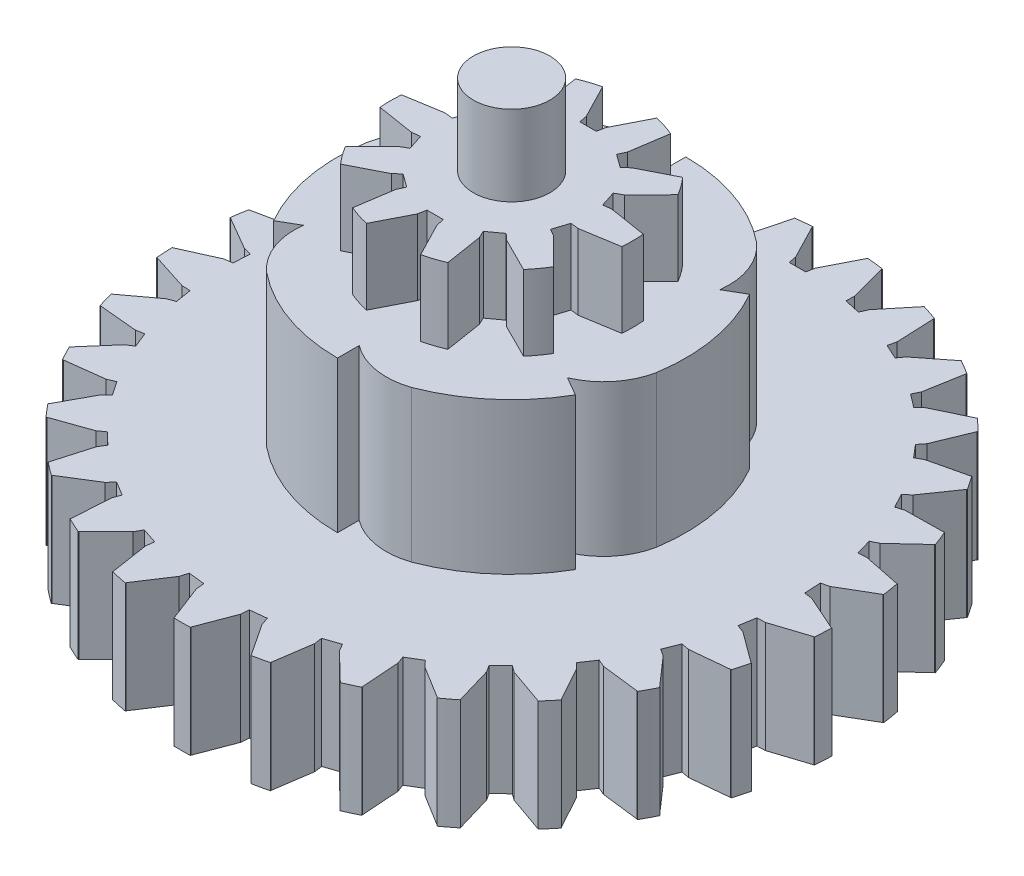
SolidWorks part; units mm, degrees
ref_plane "Front Plane" through (0, 0, 0) normal (0, 0, 1) x (1, 0, 0)
ref_plane "Top Plane" through (0, 0, 0) normal (0, 1, 0) x (1, 0, 0)
ref_plane "Right Plane" through (0, 0, 0) normal (1, 0, 0) x (0, 0, -1)
sketch "Sketch1" plane through (0, 0, 0) normal (0, 1, 0) x (1, 0, 0)
  circle A0 centre (-83.1207, 52.7325) radius 4.5085
extrude "Boss-Extrude1" add sketch "Sketch1" along normal blind 2.794
sketch "Sketch2" plane through (0, 2.794, 0) normal (0, 1, 0) x (1, 0, 0)
  circle A0 centre (-83.1207, 52.7325) radius 1.4224
extrude "Boss-Extrude2" add sketch "Sketch2" along normal blind 2.9845
sketch "Sketch3" plane through (0, 2.794, 0) normal (0, 1, 0) x (1, 0, 0)
  line L0 (-83.1207, 55.5745) -> (-82.8159, 55.5745)
  line L1 (-83.1207, 55.5745) -> (-83.4255, 55.5745)
  line L2 (-83.4255, 55.5745) -> (-83.4853, 55.8734)
  line L3 (-82.8159, 55.5745) -> (-82.7574, 55.8745)
  line L4 (-82.7574, 55.8745) -> (-82.1099, 57.1432)
  line L5 (-83.4853, 55.8734) -> (-84.1407, 57.1427)
  line L6 (-83.1207, 52.7325) -> (-83.1207, 57.241)
  line L7 (-84.1407, 57.1427) -> (-84.2034, 57.9061)
  line L8 (-84.2034, 57.9061) -> (-82.0598, 57.9061)
  line L9 (-82.0598, 57.9061) -> (-82.1099, 57.1432)
  line L10 (-81.5695, 55.4878) -> (-81.3537, 56.8999)
  line L11 (-79.2215, 56.2944) -> (-79.7104, 55.7067)
  line L12 (-80.9799, 55.0609) -> (-79.7104, 55.7067)
  line L13 (-81.2036, 54.8526) -> (-80.9799, 55.0609)
  line L14 (-81.4502, 55.0317) -> (-81.2036, 54.8526)
  line L15 (-81.4502, 55.0317) -> (-81.6968, 55.2109)
  line L16 (-81.6968, 55.2109) -> (-81.5695, 55.4878)
  line L17 (-81.3537, 56.8999) -> (-80.9557, 57.5544)
  line L18 (-80.9557, 57.5544) -> (-79.2215, 56.2944)
  line L19 (-80.2462, 54.0498) -> (-79.2416, 55.0654)
  line L20 (-77.8725, 53.3223) -> (-78.6135, 53.1341)
  line L21 (-80.0202, 53.3579) -> (-78.6135, 53.1341)
  line L22 (-80.3236, 53.3208) -> (-80.0202, 53.3579)
  line L23 (-80.4178, 53.6107) -> (-80.3236, 53.3208)
  line L24 (-80.4178, 53.6107) -> (-80.512, 53.9006)
  line L25 (-80.512, 53.9006) -> (-80.2462, 54.0498)
  line L26 (-79.2416, 55.0654) -> (-78.5349, 55.3609)
  line L27 (-78.5349, 55.3609) -> (-77.8725, 53.3223)
  line L28 (-80.0209, 52.1086) -> (-78.6112, 52.3397)
  line L29 (-78.5282, 50.1248) -> (-79.2382, 50.4081)
  line L30 (-80.2447, 51.416) -> (-79.2382, 50.4081)
  line L31 (-80.512, 51.5644) -> (-80.2447, 51.416)
  line L32 (-80.4178, 51.8543) -> (-80.512, 51.5644)
  line L33 (-80.4178, 51.8543) -> (-80.3236, 52.1441)
  line L34 (-80.3236, 52.1441) -> (-80.0209, 52.1086)
  line L35 (-78.6112, 52.3397) -> (-77.8658, 52.1635)
  line L36 (-77.8658, 52.1635) -> (-78.5282, 50.1248)
  line L37 (-80.9796, 50.4058) -> (-79.7033, 49.7641)
  line L38 (-80.938, 47.9234) -> (-81.3459, 48.57)
  line L39 (-81.5678, 49.977) -> (-81.3459, 48.57)
  line L40 (-81.6968, 50.2541) -> (-81.5678, 49.977)
  line L41 (-81.4502, 50.4333) -> (-81.6968, 50.2541)
  line L42 (-81.4502, 50.4333) -> (-81.2036, 50.6124)
  line L43 (-81.2036, 50.6124) -> (-80.9796, 50.4058)
  line L44 (-79.7033, 49.7641) -> (-79.2038, 49.1834)
  line L45 (-79.2038, 49.1834) -> (-80.938, 47.9234)
  line L46 (-82.7561, 49.5916) -> (-82.1007, 48.3223)
  line L47 (-84.1816, 47.5589) -> (-84.1315, 48.3217)
  line L48 (-83.484, 49.5904) -> (-84.1315, 48.3217)
  line L49 (-83.4255, 49.8905) -> (-83.484, 49.5904)
  line L50 (-83.1207, 49.8905) -> (-83.4255, 49.8905)
  line L51 (-83.1207, 49.8905) -> (-82.8159, 49.8905)
  line L52 (-82.8159, 49.8905) -> (-82.7561, 49.5916)
  line L53 (-82.1007, 48.3223) -> (-82.038, 47.5589)
  line L54 (-82.038, 47.5589) -> (-84.1816, 47.5589)
  line L55 (-84.6719, 49.9772) -> (-84.8877, 48.5651)
  line L56 (-87.0199, 49.1705) -> (-86.5311, 49.7583)
  line L57 (-85.2615, 50.4041) -> (-86.5311, 49.7583)
  line L58 (-85.0378, 50.6124) -> (-85.2615, 50.4041)
  line L59 (-84.7912, 50.4333) -> (-85.0378, 50.6124)
  line L60 (-84.7912, 50.4333) -> (-84.5446, 50.2541)
  line L61 (-84.5446, 50.2541) -> (-84.6719, 49.9772)
  line L62 (-84.8877, 48.5651) -> (-85.2857, 47.9106)
  line L63 (-85.2857, 47.9106) -> (-87.0199, 49.1705)
  line L64 (-85.9952, 51.4152) -> (-86.9998, 50.3996)
  line L65 (-88.3689, 52.1427) -> (-87.6279, 52.3309)
  line L66 (-86.2212, 52.1071) -> (-87.6279, 52.3309)
  line L67 (-85.9178, 52.1441) -> (-86.2212, 52.1071)
  line L68 (-85.8236, 51.8543) -> (-85.9178, 52.1441)
  line L69 (-85.8236, 51.8543) -> (-85.7294, 51.5644)
  line L70 (-85.7294, 51.5644) -> (-85.9952, 51.4152)
  line L71 (-86.9998, 50.3996) -> (-87.7065, 50.104)
  line L72 (-87.7065, 50.104) -> (-88.3689, 52.1427)
  line L73 (-86.2205, 53.3563) -> (-87.6302, 53.1252)
  line L74 (-87.7132, 55.3402) -> (-87.0032, 55.0568)
  line L75 (-85.9967, 54.049) -> (-87.0032, 55.0568)
  line L76 (-85.7294, 53.9006) -> (-85.9967, 54.049)
  line L77 (-85.8236, 53.6107) -> (-85.7294, 53.9006)
  line L78 (-85.8236, 53.6107) -> (-85.9178, 53.3208)
  line L79 (-85.9178, 53.3208) -> (-86.2205, 53.3563)
  line L80 (-87.6302, 53.1252) -> (-88.3756, 53.3015)
  line L81 (-88.3756, 53.3015) -> (-87.7132, 55.3402)
  line L82 (-85.2618, 55.0592) -> (-86.5381, 55.7009)
  line L83 (-85.3034, 57.5416) -> (-84.8955, 56.895)
  line L84 (-84.6736, 55.488) -> (-84.8955, 56.895)
  line L85 (-84.5446, 55.2109) -> (-84.6736, 55.488)
  line L86 (-84.7912, 55.0317) -> (-84.5446, 55.2109)
  line L87 (-84.7912, 55.0317) -> (-85.0378, 54.8526)
  line L88 (-85.0378, 54.8526) -> (-85.2618, 55.0592)
  line L89 (-86.5381, 55.7009) -> (-87.0376, 56.2816)
  line L90 (-87.0376, 56.2816) -> (-85.3034, 57.5416)
  line L91 (-83.1207, 52.7325) -> (-83.1207, 55.5745) construction
  circle A0 centre (-83.1207, 52.7325) radius 4.5085 construction
  circle M11 centre (-83.1207, 52.7325) radius 4.5085
  dimension "D1" = 10
  dimension "D2" = 2.842
extrude "Cut-Extrude1" cut sketch "Sketch3" against normal through all contours L88 L87 L86 L85 L84 L82 M11 | L6 L0 L3 L4 M11 | L1 L6 L5 L2 M11 | L16 L15 L14 L13 L12 L10 M11 | L25 L24 L23 L22 L21 L19 M11 | L34 L33 L32 L31 L30 L28 M11 | L43 L42 L41 L40 L39 L37 M11 | L52 L51 L50 L49 L48 L46 M11 | L61 L60 L59 L58 L57 L55 M11 | L70 L69 L68 L67 L66 L64 M11 | L79 L78 L77 L76 L75 L73 M11
sketch "Sketch4" plane through (0, 0, 0) normal (0, -1, 0) x (1, 0, 0)
  circle A0 centre (-83.1207, -52.7325) radius 6.477
extrude "Boss-Extrude3" add sketch "Sketch4" along normal blind 5.6261
sketch "Sketch5" plane through (0, 0, 0) normal (0, 1, 0) x (1, 0, 0)
  line L0 (-83.1207, 58.4015) -> (-83.1207, 59.2095)
  line L6 (-78.2112, 55.567) -> (-77.5115, 55.971)
  line L7 (-78.2112, 49.898) -> (-77.5115, 49.494)
  line L8 (-83.1207, 47.0635) -> (-83.1207, 46.2555)
  line L9 (-88.0302, 49.898) -> (-88.7299, 49.494)
  line L10 (-88.0302, 55.567) -> (-88.7299, 55.971)
  line L11 (-83.1207, 52.7325) -> (-84.6382, 56.3955) construction
  circle A0 centre (-83.1207, 52.7325) radius 6.477 construction
  arc A2 (-83.1207, 58.4015) -> (-85.4488, 58.7766) centre (-84.6382, 56.3955) ccw
  arc A3 (-85.4488, 58.7766) -> (-83.1207, 59.2095) centre (-83.1207, 52.7325) cw
  arc A14 (-79.0504, 57.7708) -> (-77.5115, 55.971) centre (-83.1207, 52.7325) cw
  arc A15 (-78.2112, 55.567) -> (-79.0504, 57.7708) centre (-80.7072, 55.8782) ccw
  arc A16 (-76.7223, 51.7267) -> (-77.5115, 49.494) centre (-83.1207, 52.7325) cw
  arc A17 (-78.2112, 49.898) -> (-76.7223, 51.7267) centre (-79.1897, 52.2152) ccw
  arc A18 (-80.7926, 46.6884) -> (-83.1207, 46.2555) centre (-83.1207, 52.7325) cw
  arc A19 (-83.1207, 47.0635) -> (-80.7926, 46.6884) centre (-81.6032, 49.0695) ccw
  arc A20 (-87.191, 47.6942) -> (-88.7299, 49.494) centre (-83.1207, 52.7325) cw
  arc A21 (-88.0302, 49.898) -> (-87.191, 47.6942) centre (-85.5342, 49.5868) ccw
  arc A22 (-89.5191, 53.7383) -> (-88.7299, 55.971) centre (-83.1207, 52.7325) cw
  arc A23 (-88.0302, 55.567) -> (-89.5191, 53.7383) centre (-87.0517, 53.2498) ccw
  point P0 (-89.5191, 53.7383)
  dimension "D1" = 6
  dimension "D2" = 3.9649
extrude "Cut-Extrude2" cut sketch "Sketch5" against normal through all contours L0 A3 A2 | A23 A22 L10 | A21 A20 L9 | A19 A18 L8 | A17 A16 L7 | A15 A14 L6
sketch "Sketch6" plane through (0, -5.6261, 0) normal (0, -1, 0) x (1, 0, 0)
  circle A0 centre (-83.1207, -52.7325) radius 12.2619
extrude "Boss-Extrude4" add sketch "Sketch6" along normal blind 4.1275 contours A0
sketch "Sketch7" plane through (0, -9.7536, 0) normal (0, -1, 0) x (1, 0, 0)
  circle A0 centre (-83.1207, -52.7325) radius 1.4224
extrude "Boss-Extrude5" add sketch "Sketch7" along normal blind 3.302 contours A0
ref_plane "Plane1" through (0, 0, -40.4622) normal (0, 0, 1) x (1, 0, 0)
sketch "Sketch11" plane through (0, -5.6261, 0) normal (0, 1, 0) x (1, 0, 0)
  line L0 (-83.1207, 52.7325) -> (-83.1207, 64.9943)
  line L1 (-83.1207, 63.3604) -> (-82.8159, 63.3604)
  line L2 (-83.1207, 63.3604) -> (-83.4255, 63.3604)
  line L3 (-83.4255, 63.3604) -> (-83.4853, 63.6593)
  line L4 (-82.8159, 63.3604) -> (-82.7574, 63.6604)
  line L5 (-82.7574, 63.6604) -> (-82.1099, 64.9291)
  line L6 (-83.4853, 63.6593) -> (-84.1407, 64.9286)
  line L7 (-84.1407, 64.9286) -> (-84.2034, 65.692)
  line L9 (-82.0598, 65.692) -> (-82.1099, 64.9291)
  line L10 (-84.2034, 65.692) -> (-82.0598, 65.692)
  circle A0 centre (-83.1207, 52.7325) radius 12.2619 construction
extrude "Cut-Extrude4" cut sketch "Sketch11" against normal through all and the other way through all
pattern_circular "CirPattern3" count 29 over 360 about axis through (-83.1207, 0, -52.7325) along (0, 1, 0) of "Cut-Extrude4"
